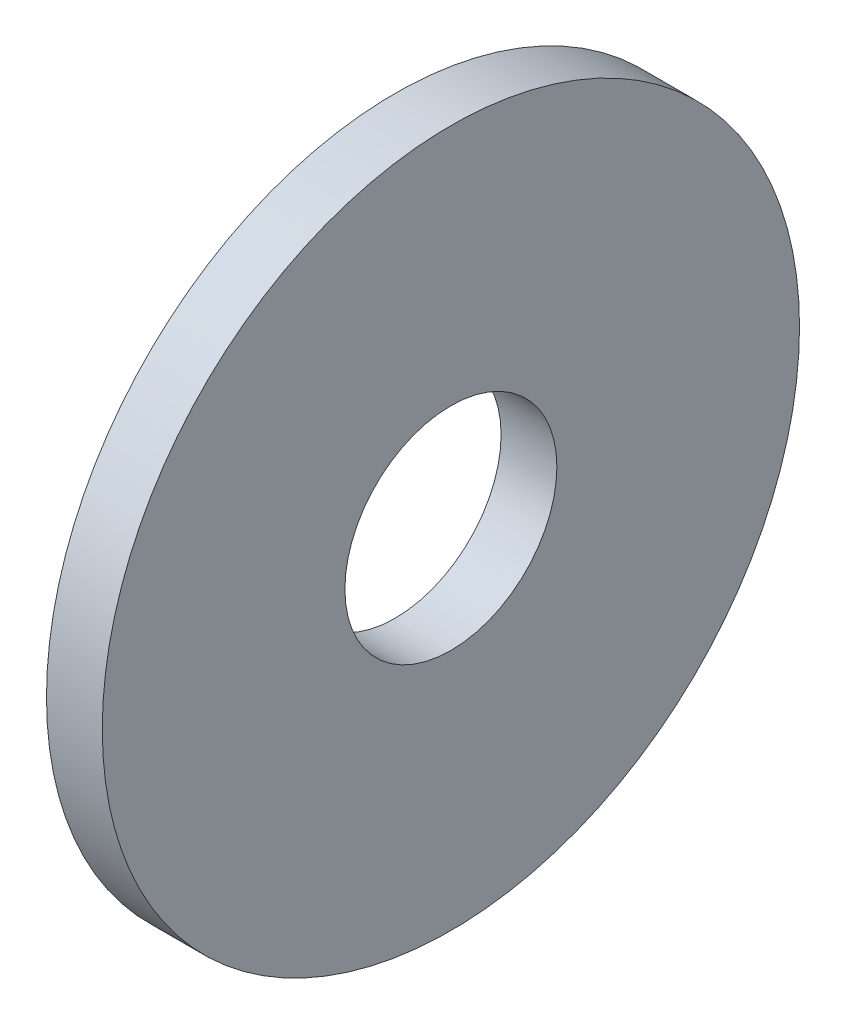
SolidWorks part; units mm, degrees
ref_plane "Front" through (0, 0, 0) normal (0, 0, 1) x (1, 0, 0)
ref_plane "Top" through (0, 0, 0) normal (0, 1, 0) x (1, 0, 0)
ref_plane "Right" through (0, 0, 0) normal (1, 0, 0) x (0, 0, -1)
ref_plane "Plane1" through (0, 0, 0) normal (0, 0, -1) x (-1, 0, 0)
sketch "Sketch1" plane through (0, 0, 0) normal (0, 0, -1) x (-1, 0, 0)
  line L0 (-1.778, 3.3782) -> (0, 3.3782)
  line L1 (0, 3.3782) -> (0, 11.1125)
  line L2 (0, 11.1125) -> (-1.778, 11.1125)
  line L3 (-1.778, 11.1125) -> (-1.778, 3.3782)
  line L4 (-1.778, 0) -> (0, 0) construction
revolve "Revolve1" add sketch "Sketch1" angle 360 about L4
